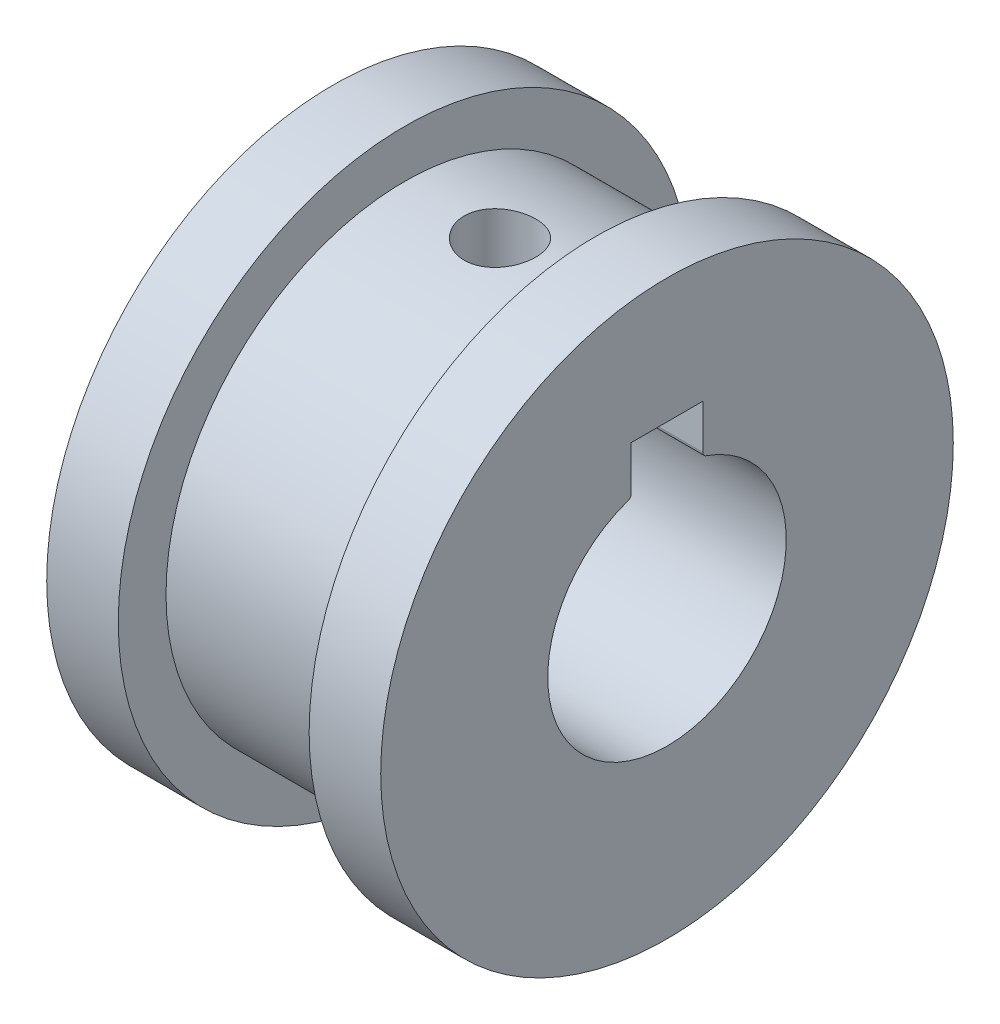
SolidWorks part; units mm, degrees
ref_plane "Piano frontale" through (0, 0, 0) normal (0, 0, 1) x (1, 0, 0)
ref_plane "Piano superiore" through (0, 0, 0) normal (0, 1, 0) x (1, 0, 0)
ref_plane "Piano destro" through (0, 0, 0) normal (1, 0, 0) x (0, 0, -1)
sketch "Sketch1" plane through (0, 0, 0) normal (1, 0, 0) x (0, 0, -1)
  circle A0 centre (0, 0) radius 10
  dimension "D1" = 20
extrude "Boss-Extrude1" add sketch "Sketch1" along normal blind 8
sketch "Sketch2" plane through (8, 0, 0) normal (1, 0, 0) x (0, 0, -1)
  line L0 (0, 4.7697) -> (0, 10) construction
  line L1 (0, 6.7697) -> (0, 4.7697) construction
  line L2 (-1.5, 6.7697) -> (1.5, 6.7697)
  line L3 (-1.5, 6.7697) -> (-1.5, 4.9143)
  line L5 (1.5, 6.7697) -> (1.5, 4.9143)
  arc A0 (-1.6346, 4.7253) -> (1.6346, 4.7253) centre (0, 0) ccw
  circle A1 centre (0, 0) radius 10 construction
  arc A2 (-1.6346, 4.7253) -> (-1.5, 4.9143) centre (-1.7, 4.9143) ccw
  arc A3 (1.6346, 4.7253) -> (1.5, 4.9143) centre (1.7, 4.9143) cw
  point P14 (-1.5, 4.7697)
  dimension "D1" = 10
  dimension "D4" = 0.2
  dimension "D5" = 0.2
  dimension "D2" = 3
  dimension "D3" = 2
sketch "Sketch3" plane through (8, 0, 0) normal (1, 0, 0) x (0, 0, -1)
  circle A0 centre (0, 0) radius 12
  dimension "D1" = 24
extrude "Boss-Extrude2" add sketch "Sketch3" along normal blind 3
sketch "Sketch4" plane through (0, 0, 0) normal (-1, 0, 0) x (0, 0, 1)
  circle A0 centre (0, 0) radius 12
  dimension "D1" = 24
extrude "Boss-Extrude3" add sketch "Sketch4" along normal blind 3
extrude "Cut-Extrude2" cut sketch "Sketch2" against normal blind 11 and the other way blind 3
sketch "Sketch6" plane through (0, 6.7697, 0) normal (0, -1, 0) x (1, 0, 0)
  line L0 (-3, 0) -> (11, 0) construction
  line L1 (-3, -1.5) -> (-3, 1.5) construction
  line L2 (11, -1.5) -> (11, 1.5) construction
  circle A0 centre (4, 0) radius 1.5
  dimension "D1" = 3
extrude "Cut-Extrude3" cut sketch "Sketch6" against normal blind 5
